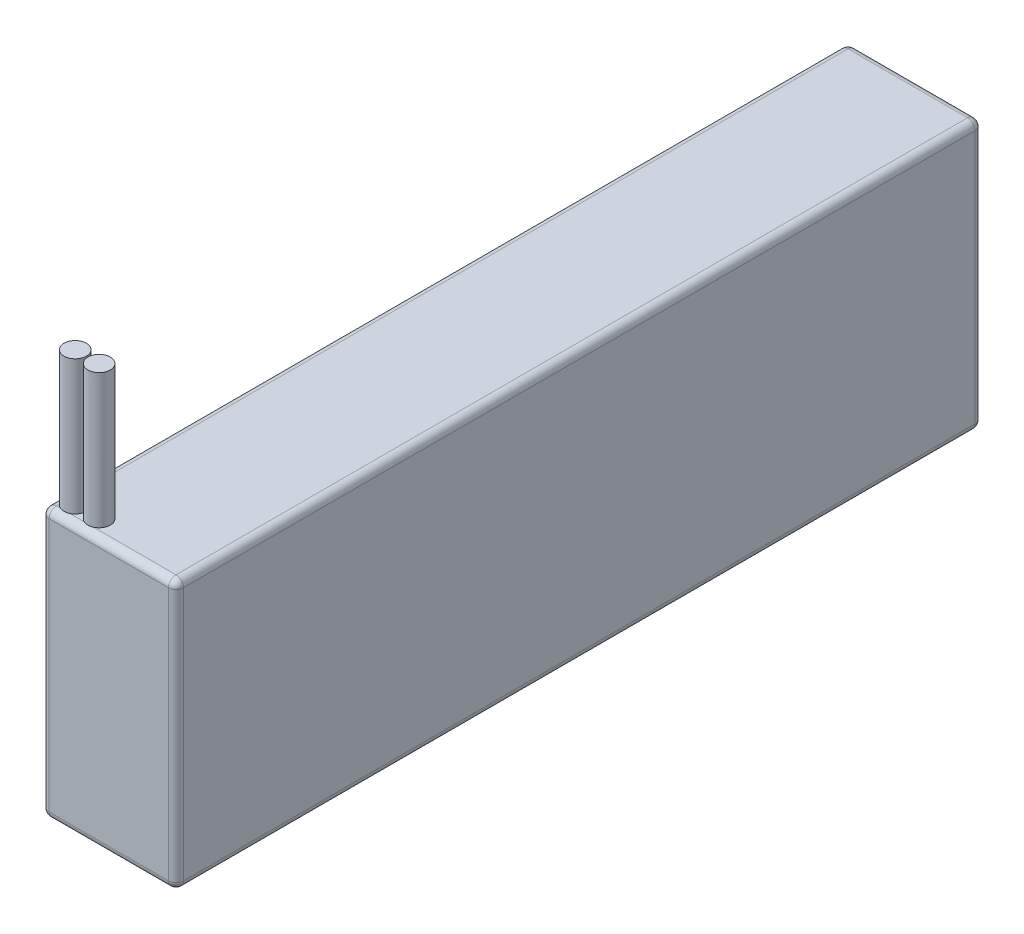
SolidWorks part; units mm, degrees
ref_plane "Front Plane" through (0, 0, 0) normal (0, 0, 1) x (1, 0, 0)
ref_plane "Top Plane" through (0, 0, 0) normal (0, 1, 0) x (1, 0, 0)
ref_plane "Right Plane" through (0, 0, 0) normal (1, 0, 0) x (0, 0, -1)
sketch "Sketch1" plane through (0, 0, 0) normal (1, 0, 0) x (0, 0, -1)
  line L1 (-68.58, -22.86) -> (68.58, -22.86)
  line L2 (-68.58, -22.86) -> (-68.58, 22.86)
  line L3 (-68.58, 22.86) -> (68.58, 22.86)
  line L4 (68.58, -22.86) -> (68.58, 22.86)
  line L5 (-68.58, -22.86) -> (68.58, 22.86) construction
  line L6 (-68.58, 22.86) -> (68.58, -22.86) construction
  point P0 (0, 0)
  dimension "D1" = 137.16
  dimension "D2" = 45.72
extrude "Boss-Extrude1" add sketch "Sketch1" along normal blind 22.86
fillet "Fillet1" radius 1.27 12 edges at (22.86, -22.86, 0) (0, -22.86, 0) (22.86, 0, 68.58) (11.43, -22.86, 68.58) (0, 0, 68.58) (11.43, -22.86, -68.58) (22.86, 0, -68.58) (0, 0, -68.58) (11.43, 22.86, -68.58) (22.86, 22.86, 0) (11.43, 22.86, 68.58) (0, 22.86, 0)
sketch "Sketch2" plane through (0, 22.86, 0) normal (0, 1, 0) x (1, 0, 0)
  circle A0 centre (2.7226, -65.5854) radius 1.905
  circle A1 centre (6.7866, -65.5854) radius 1.905
  dimension "D1" = 3.81
  dimension "D2" = 3.81
  dimension "D3" = 4.064
extrude "Boss-Extrude2" add sketch "Sketch2" along normal blind 22.86
